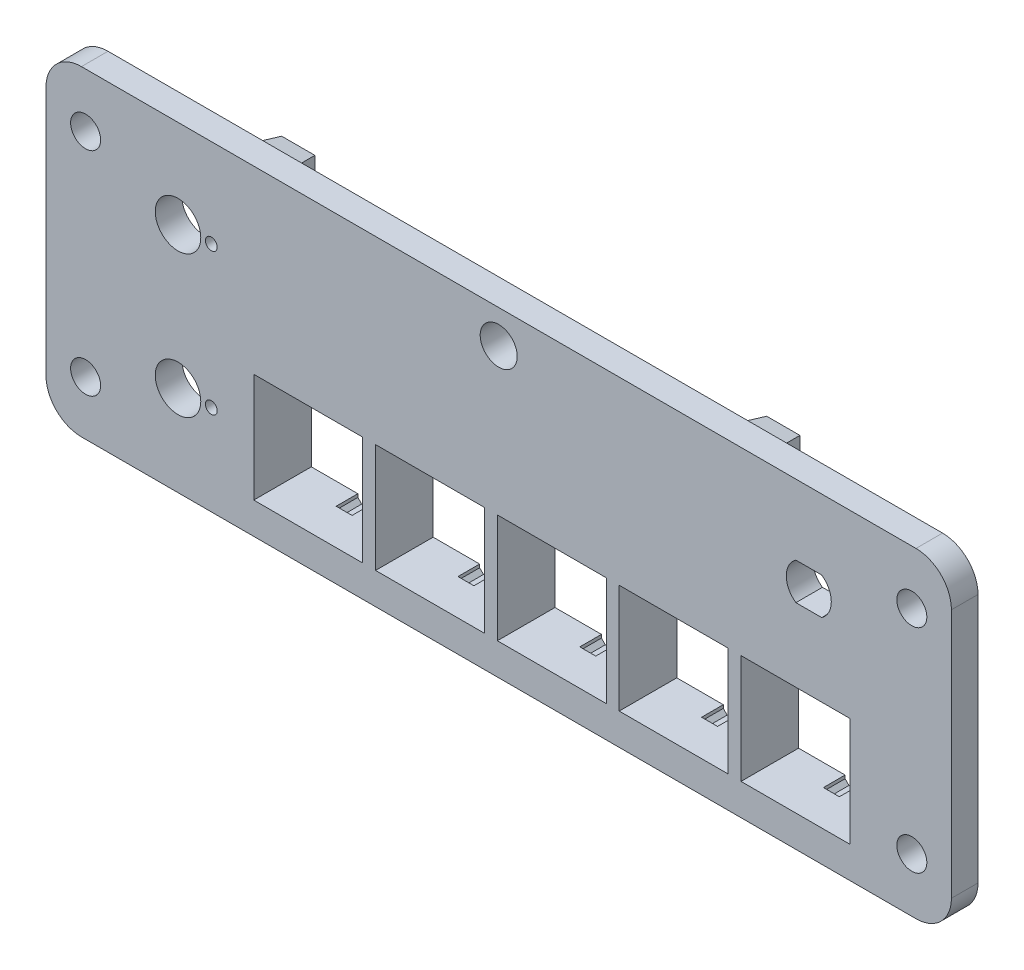
SolidWorks part; units mm, degrees
material "PET"
ref_plane "Front Plane" through (0, 0, 0) normal (0, 0, 1) x (1, 0, 0)
ref_plane "Top Plane" through (0, 0, 0) normal (0, 1, 0) x (1, 0, 0)
ref_plane "Right Plane" through (0, 0, 0) normal (1, 0, 0) x (0, 0, -1)
sketch "Sketch1" plane through (0, 0, 0) normal (0, 0, 1) x (1, 0, 0)
  line L4 (-59.817, -45.974) -> (59.817, -45.974)
  line L5 (64.897, -40.894) -> (64.897, -5.08)
  line L6 (59.817, 0) -> (-59.817, 0)
  line L7 (-64.897, -5.08) -> (-64.897, -40.894)
  line L8 (-59.817, -45.974) -> (59.817, -45.974)
  line L9 (64.897, -40.894) -> (64.897, -5.08)
  line L10 (59.817, 0) -> (-59.817, 0)
  line L11 (-64.897, -5.08) -> (-64.897, -40.894)
  arc A4 (-64.897, -40.894) -> (-59.817, -45.974) centre (-59.817, -40.894) ccw
  arc A5 (59.817, -45.974) -> (64.897, -40.894) centre (59.817, -40.894) ccw
  arc A6 (64.897, -5.08) -> (59.817, 0) centre (59.817, -5.08) ccw
  arc A7 (-59.817, 0) -> (-64.897, -5.08) centre (-59.817, -5.08) ccw
  arc A8 (-64.897, -40.894) -> (-59.817, -45.974) centre (-59.817, -40.894) ccw
  arc A9 (59.817, -45.974) -> (64.897, -40.894) centre (59.817, -40.894) ccw
  arc A10 (64.897, -5.08) -> (59.817, 0) centre (59.817, -5.08) ccw
  arc A11 (-59.817, 0) -> (-64.897, -5.08) centre (-59.817, -5.08) ccw
  dimension "D1" = 0
extrude "Boss-Extrude1" add sketch "Sketch1" along normal blind 3.81
sketch "Sketch5" plane through (0, 0, 3.81) normal (0, 0, 1) x (1, 0, 0)
  line L4 (52.07, -41.91) -> (52.07, -25.4)
  line L5 (50.8, -24.13) -> (-35.56, -24.13)
  line L6 (-36.83, -25.4) -> (-36.83, -41.91)
  line L7 (-35.56, -43.18) -> (50.8, -43.18)
  line L8 (52.07, -41.91) -> (52.07, -25.4)
  line L9 (50.8, -24.13) -> (-35.56, -24.13)
  line L10 (-36.83, -25.4) -> (-36.83, -41.91)
  line L11 (-35.56, -43.18) -> (50.8, -43.18)
  arc A4 (52.07, -25.4) -> (50.8, -24.13) centre (50.8, -25.4) ccw
  arc A5 (-35.56, -24.13) -> (-36.83, -25.4) centre (-35.56, -25.4) ccw
  arc A6 (-36.83, -41.91) -> (-35.56, -43.18) centre (-35.56, -41.91) ccw
  arc A7 (50.8, -43.18) -> (52.07, -41.91) centre (50.8, -41.91) ccw
  arc A8 (52.07, -25.4) -> (50.8, -24.13) centre (50.8, -25.4) ccw
  arc A9 (-35.56, -24.13) -> (-36.83, -25.4) centre (-35.56, -25.4) ccw
  arc A10 (-36.83, -41.91) -> (-35.56, -43.18) centre (-35.56, -41.91) ccw
  arc A11 (50.8, -43.18) -> (52.07, -41.91) centre (50.8, -41.91) ccw
  dimension "D1" = 0
extrude "Cut-Extrude1" cut sketch "Sketch5" against normal through all
hole_wizard "#6 Clearance Hole1" positions "Sketch7" profile "Sketch6" hole size "#6" standard "ANSI Inch" end condition through all
sketch "Sketch7" plane through (0, 0, 3.81) normal (0, 0, 1) x (1, 0, 0)
  point P0 (59.2201, -7.747)
  point P3 (59.2201, -38.227)
  point P6 (-59.2201, -38.227)
  point P9 (-59.2201, -7.747)
sketch "Sketch6" plane through (59.2201, -7.747, 3.81) normal (1, 0, 0) x (0, -1, 0)
  line L0 (0, 0) -> (0, 3.81)
  line L1 (0, 3.81) -> (2.1526, 3.81)
  line L2 (2.1526, 3.81) -> (2.1526, 0)
  line L5 (2.1526, 0) -> (0, 0)
  line L11 (0, -6.35) -> (0, 107.95) construction
  dimension "Thru Hole Dia." = 4.3053
  dimension "Thru Hole Depth" = 3.81
sketch "Sketch8" plane through (0, 0, 3.81) normal (0, 0, 1) x (1, 0, 0)
  line L1 (42.5986, -10.0584) -> (46.3014, -10.0584)
  line L2 (44.45, -15.3416) -> (44.45, -10.0584)
  line L3 (46.3014, -15.3416) -> (42.5986, -15.3416)
  arc A0 (42.5986, -10.0584) -> (42.5986, -15.3416) centre (44.45, -12.7) ccw
  arc A1 (46.3014, -15.3416) -> (46.3014, -10.0584) centre (44.45, -12.7) ccw
  point P9 (44.45, -12.7)
  point P12 (44.45, -15.3416)
  dimension "D1" = 6.4516
  dimension "D2" = 5.2832
extrude "Cut-Extrude2" cut sketch "Sketch8" against normal through all contours L3 A1 L1 L2 | L1 A0 L3 L2
sketch "Sketch9" plane through (0, 0, 3.81) normal (0, 0, 1) x (1, 0, 0)
  line L2 (38.6715, -12.7) -> (50.2285, -12.7) construction
  line L3 (-45.974, -12.7) -> (-45.974, -33.02) construction
  line L4 (44.45, -20.1151) -> (44.45, -5.2849) construction
  line L5 (-45.974, -22.86) -> (-64.897, -22.86) construction
  line L6 (-64.897, -5.08) -> (-64.897, -40.894) construction
  circle A0 centre (-45.974, -12.7) radius 3.2639
  circle A1 centre (-41.1988, -12.7) radius 0.8509
  circle A2 centre (-45.974, -33.02) radius 3.2639
  circle A3 centre (-41.1988, -33.02) radius 0.8509
  circle A4 centre (-45.974, -33.02) radius 3.2639
  point P0 (-45.974, -12.7)
  point P4 (-45.974, -33.02)
  dimension "D1" = 6.5278
  dimension "D2" = 1.7018
  dimension "D3" = 4.7752
extrude "Cut-Extrude3" cut sketch "Sketch9" against normal through all contours A2 | A3 | A0 | A1
hole_wizard "#6-32 Tapped Hole1" positions "Sketch11" profile "Sketch10" tap size "#6-32" standard "ANSI Inch" end condition through all
sketch "Sketch11" plane through (0, 0, 3.81) normal (0, 0, 1) x (1, 0, 0)
  point P0 (0, -4.7575)
sketch "Sketch10" plane through (0, -4.7575, 3.81) normal (1, 0, 0) x (0, -1, 0)
  line L0 (0, 0) -> (0, 3.81)
  line L1 (0, 3.81) -> (1.3525, 3.81)
  line L2 (1.3525, 3.81) -> (1.3525, 0)
  line L5 (1.3525, 0) -> (0, 0)
  line L11 (0, -6.35) -> (0, 107.95) construction
  dimension "Thru Tap Drill Dia." = 2.7051
  dimension "Thru Tap Drill Depth" = 3.81
cosmetic thread "Hole Thread1" parameters "D2"=3.5052
sketch "Sketch12" plane through (0, 0, 3.81) normal (0, 0, 1) x (1, 0, 0)
  line L0 (5.95, -21.748) -> (11.95, -21.748) construction
  line L1 (8.95, -21.748) -> (-9, -21.748)
  line L2 (8.95, -21.748) -> (8.95, -9.748)
  line L3 (8.95, -9.748) -> (-9, -9.748)
  line L4 (-9, -21.748) -> (-9, -9.748)
  line L5 (8.95, -21.748) -> (-9, -9.748) construction
  line L6 (8.95, -9.748) -> (-9, -21.748) construction
  line L7 (-9, -22.748) -> (-9, -8.748) construction
  line L11 (5.95, -9.748) -> (-5.95, -9.748) construction
  point P4 (-0.025, -15.748)
extrude "Cut-Extrude4" [suppressed] cut sketch "Sketch12" against normal through all
fillet "Fillet1" [suppressed] radius 1.651
hole_wizard "CSK for #4 Flat Head Machine Screw (100)1" [suppressed] positions "Sketch14" profile "Sketch13" countersink size "#4" standard "ANSI Inch"
sketch "Sketch14" plane through (0, 0, 3.175) normal (0, 0, 1) x (1, 0, 0)
  point P0 (-15, -15.748)
  point P3 (15, -15.748)
sketch "Sketch13" plane through (-15, -15.748, 3.175) normal (1, 0, 0) x (0, -1, 0)
  line L0 (0, 0) -> (0, 3.175)
  line L1 (0, 3.175) -> (1.7272, 3.175)
  line L2 (1.7272, 3.175) -> (1.7272, 1.2024)
  line L3 (1.7272, 1.2024) -> (3.1602, 0)
  line L5 (3.1602, 0) -> (0, 0)
  line L6 (-1.7272, 1.2024) -> (-3.1602, 0) construction
  line L11 (0, -6.35) -> (0, 107.95) construction
  dimension "Thru Hole Dia." = 3.4544
  dimension "Thru Hole Depth" = 3.175
  dimension "Near C'Sink Dia." = 6.3204
  dimension "Near C'Sink Angle" = 100
sketch "Sketch15" plane through (0, 0, 3.81) normal (0, 0, 1) x (1, 0, 0)
  line L0 (44.45, -12.7) -> (44.45, -18.415) construction
  line L1 (44.45, -18.415) -> (44.45, -19.177) construction
  line L2 (47.8092, -17.3235) -> (48.2571, -17.94) construction
  line L3 (44.45, -12.7) -> (47.8092, -17.3235) construction
  line L4 (49.8853, -14.466) -> (50.61, -14.7015) construction
  line L5 (44.45, -12.7) -> (49.8853, -14.466) construction
  line L6 (49.8853, -10.934) -> (50.61, -10.6985) construction
  line L7 (44.45, -12.7) -> (49.8853, -10.934) construction
  line L8 (47.8092, -8.0765) -> (48.2571, -7.46) construction
  line L9 (44.45, -12.7) -> (47.8092, -8.0765) construction
  line L10 (44.45, -12.7) -> (44.45, -18.415) construction
  line L11 (44.45, -12.7) -> (47.8092, -17.3235) construction
  line L12 (48.2571, -17.94) -> (50.2891, -17.94) construction
  line L16 (48.2571, -5.8306) -> (50.2891, -5.8306) construction
  line L17 (52.642, -9.655) -> (50.61, -9.655) construction
  line L18 (50.61, -13.8984) -> (52.642, -13.8984) construction
  line L19 (45.3869, -19.177) -> (43.5131, -19.177) construction
  line L20 (44.45, -12.7) -> (44.45, -21.7325) construction
  line L21 (52.467, -21.7325) -> (36.433, -21.7325) construction
  line L22 (-45.974, -33.02) -> (-45.974, -40.64) construction
  line L23 (-45.974, -38.735) -> (-45.974, -27.305) construction
  line L24 (-40.2446, -40.64) -> (-51.7034, -40.64) construction
  line L25 (-45.974, -12.7) -> (-45.974, -20.32) construction
  line L26 (-45.974, -18.415) -> (-45.974, -6.985) construction
  line L27 (-39.5334, -20.32) -> (-52.4146, -20.32) construction
  arc A0 (42.684, -18.1353) -> (46.216, -7.2647) centre (44.45, -12.7) ccw construction
  text T0 "F" font "GordonURWCon" height in points 9
  text T1 "U" font "GordonURWCon" height in points 9
  text T2 "A" font "GordonURWCon" height in points 9
  text T3 "I" font "GordonURWCon" height in points 9
  text T4 "N" font "GordonURWCon" height in points 9
  text T5 "DIS TYPE" font "GordonURWMed" height in points 9
  text T6 "AUDIO" font "GordonURWMed" height in points 12
  text T7 "DMR" font "GordonURWMed" height in points 12
  point P23 (49.2731, -17.94)
  point P33 (44.45, -21.7325)
  point P43 (44.45, -19.177)
  point P45 (-45.974, -40.64)
  point P54 (-45.974, -20.32)
  dimension "D1" = 5
  dimension "D4" = 7.62
  dimension "D5" = 0.762
  dimension "D2" = 36
  dimension "D3" = 2.032
wrap "Wrap1" [suppressed] sketch "Sketch15" source sketch "Sketch15"
sketch "Sketch16" plane through (0, 0, 3.81) normal (0, 0, 1) x (1, 0, 0)
  line L0 (11.2625, -24.13) -> (16.025, -24.13) construction
  line L1 (13.6437, -24.13) -> (13.6437, -19.3675) construction
  line L2 (7.1437, -43.18) -> (7.1437, -2.54) construction
  line L3 (-39.37, -2.54) -> (34.925, -2.54) construction
  line L9 (50.3555, -41.4655) -> (50.3555, -25.8445)
  line L10 (50.3555, -25.8445) -> (34.7345, -25.8445)
  line L11 (34.7345, -25.8445) -> (34.7345, -41.4655)
  line L12 (34.7345, -41.4655) -> (50.3555, -41.4655)
  line L13 (50.3555, -41.4655) -> (50.3555, -25.8445)
  line L14 (50.3555, -25.8445) -> (34.7345, -25.8445)
  line L15 (34.7345, -25.8445) -> (34.7345, -41.4655)
  line L16 (34.7345, -41.4655) -> (50.3555, -41.4655)
  line L17 (-2.032, -41.4655) -> (-2.032, -25.8445)
  line L18 (-2.032, -25.8445) -> (-17.653, -25.8445)
  line L19 (-17.653, -25.8445) -> (-17.653, -41.4655)
  line L20 (-17.653, -41.4655) -> (-2.032, -41.4655)
  line L21 (-2.032, -41.4655) -> (-2.032, -25.8445)
  line L22 (32.893, -41.4655) -> (32.893, -25.8445)
  line L23 (32.893, -25.8445) -> (17.272, -25.8445)
  line L24 (17.272, -25.8445) -> (17.272, -41.4655)
  line L25 (17.272, -41.4655) -> (32.893, -41.4655)
  line L26 (32.893, -41.4655) -> (32.893, -25.8445)
  line L27 (32.893, -25.8445) -> (17.272, -25.8445)
  line L28 (17.272, -25.8445) -> (17.272, -41.4655)
  line L29 (17.272, -41.4655) -> (32.893, -41.4655)
  line L30 (-2.032, -25.8445) -> (-17.653, -25.8445)
  line L31 (-17.653, -25.8445) -> (-17.653, -41.4655)
  line L32 (-17.653, -41.4655) -> (-2.032, -41.4655)
  line L34 (-39.37, -43.18) -> (-39.37, -2.54) construction
  line L35 (15.4305, -41.4655) -> (15.4305, -25.8445)
  line L36 (15.4305, -25.8445) -> (-0.1905, -25.8445)
  line L37 (-0.1905, -25.8445) -> (-0.1905, -41.4655)
  line L38 (-0.1905, -41.4655) -> (15.4305, -41.4655)
  line L39 (15.4305, -41.4655) -> (15.4305, -25.8445)
  line L40 (15.4305, -25.8445) -> (-0.1905, -25.8445)
  line L41 (-0.1905, -25.8445) -> (-0.1905, -41.4655)
  line L42 (-0.1905, -41.4655) -> (15.4305, -41.4655)
  line L43 (-39.37, -43.18) -> (53.6575, -43.18)
  line L44 (-39.37, -43.18) -> (-39.37, -24.13)
  line L45 (-39.37, -24.13) -> (11.2625, -24.13)
  line L46 (-19.4945, -41.4655) -> (-19.4945, -25.8445)
  line L47 (-19.4945, -25.8445) -> (-35.1155, -25.8445)
  line L48 (-35.1155, -25.8445) -> (-35.1155, -41.4655)
  line L49 (-35.1155, -41.4655) -> (-19.4945, -41.4655)
  line L50 (-19.4945, -41.4655) -> (-19.4945, -25.8445)
  line L51 (-19.4945, -25.8445) -> (-35.1155, -25.8445)
  line L52 (-35.1155, -25.8445) -> (-35.1155, -41.4655)
  line L53 (-35.1155, -41.4655) -> (-19.4945, -41.4655)
  line L54 (53.6575, -43.18) -> (53.6575, -24.13)
  line L55 (53.6575, -24.13) -> (53.6575, -43.18) construction
  line L56 (44.925, -24.13) -> (53.6575, -24.13) construction
  line L57 (53.6575, -43.18) -> (-39.37, -43.18) construction
  line L58 (16.025, -24.13) -> (53.6575, -24.13)
  line L59 (34.925, -2.54) -> (30.1625, -2.54)
  line L60 (34.925, -2.54) -> (34.925, -7.3025)
  line L61 (34.925, -7.3025) -> (30.1625, -7.3025)
  line L62 (30.1625, -2.54) -> (30.1625, -7.3025)
  line L63 (-39.37, -2.54) -> (-34.6075, -2.54)
  line L64 (-39.37, -2.54) -> (-39.37, -7.3025)
  line L65 (-39.37, -7.3025) -> (-34.6075, -7.3025)
  line L66 (-34.6075, -2.54) -> (-34.6075, -7.3025)
  line L67 (11.2625, -19.3675) -> (16.025, -19.3675)
  line L68 (11.2625, -19.3675) -> (11.2625, -24.13)
  line L70 (16.025, -19.3675) -> (16.025, -24.13)
  dimension "D6" = 4.7625
  dimension "D7" = 6.5
  dimension "D1" = 0.762
  dimension "D2" = 0.762
  dimension "D3" = 0.762
  dimension "D4" = 0.762
  dimension "D5" = 0.762
extrude "Boss-Extrude2" add sketch "Sketch16" against normal up to surface (8.255 mm away) contours L68 L45 L44 L43 L54 L58 L70 L67
sketch "Sketch17" plane through (0, 0, -4.445) normal (0, 0, -1) x (-1, 0, 0)
  line L44 (-37.8778, -26.0985) -> (-37.8778, -25.3801)
  line L45 (-37.8778, -25.3801) -> (-38.4293, -24.8285)
  line L46 (-38.4293, -24.8285) -> (-39.6122, -24.8285)
  line L47 (-39.6122, -24.8285) -> (-40.1638, -25.3801)
  line L48 (-40.1638, -25.3801) -> (-40.1638, -26.0985)
  line L49 (-40.1638, -26.0985) -> (-44.9263, -26.0985)
  line L50 (-44.9263, -26.0985) -> (-44.9263, -25.3801)
  line L51 (-44.9263, -25.3801) -> (-45.4778, -24.8285)
  line L52 (-45.4778, -24.8285) -> (-46.6607, -24.8285)
  line L53 (-46.6607, -24.8285) -> (-47.2123, -25.3801)
  line L54 (-47.2123, -25.3801) -> (-47.2123, -26.0985)
  line L55 (-47.2123, -26.0985) -> (-50.1015, -26.0985)
  line L56 (-50.1015, -26.0985) -> (-50.1015, -41.2115)
  line L57 (-50.1015, -41.2115) -> (-43.688, -41.2115)
  line L58 (-43.688, -41.2115) -> (-43.688, -41.9299)
  line L59 (-43.688, -41.9299) -> (-43.1364, -42.4815)
  line L60 (-43.1364, -42.4815) -> (-41.9536, -42.4815)
  line L61 (-41.9536, -42.4815) -> (-41.402, -41.9299)
  line L62 (-41.402, -41.9299) -> (-41.402, -41.2115)
  line L63 (-41.402, -41.2115) -> (-34.9885, -41.2115)
  line L64 (-34.9885, -41.2115) -> (-34.9885, -26.0985)
  line L65 (-34.9885, -26.0985) -> (-37.8778, -26.0985)
  line L66 (-37.8778, -26.0985) -> (-37.8778, -25.3801)
  line L67 (-37.8778, -25.3801) -> (-38.4293, -24.8285)
  line L68 (-38.4293, -24.8285) -> (-39.6122, -24.8285)
  line L69 (-39.6122, -24.8285) -> (-40.1638, -25.3801)
  line L70 (-40.1638, -25.3801) -> (-40.1638, -26.0985)
  line L71 (-40.1638, -26.0985) -> (-44.9263, -26.0985)
  line L72 (-44.9263, -26.0985) -> (-44.9263, -25.3801)
  line L73 (-44.9263, -25.3801) -> (-45.4778, -24.8285)
  line L74 (-45.4778, -24.8285) -> (-46.6607, -24.8285)
  line L75 (-46.6607, -24.8285) -> (-47.2123, -25.3801)
  line L76 (-47.2123, -25.3801) -> (-47.2123, -26.0985)
  line L77 (-47.2123, -26.0985) -> (-50.1015, -26.0985)
  line L78 (-50.1015, -26.0985) -> (-50.1015, -41.2115)
  line L79 (-50.1015, -41.2115) -> (-43.688, -41.2115)
  line L80 (-43.688, -41.2115) -> (-43.688, -41.9299)
  line L81 (-43.688, -41.9299) -> (-43.1364, -42.4815)
  line L82 (-43.1364, -42.4815) -> (-41.9536, -42.4815)
  line L83 (-41.9536, -42.4815) -> (-41.402, -41.9299)
  line L84 (-41.402, -41.9299) -> (-41.402, -41.2115)
  line L85 (-41.402, -41.2115) -> (-34.9885, -41.2115)
  line L86 (-34.9885, -41.2115) -> (-34.9885, -26.0985)
  line L87 (-34.9885, -26.0985) -> (-37.8778, -26.0985)
  line L88 (14.5097, -26.0985) -> (14.5097, -25.3801)
  line L89 (14.5097, -25.3801) -> (13.9582, -24.8285)
  line L90 (13.9582, -24.8285) -> (12.7753, -24.8285)
  line L91 (12.7753, -24.8285) -> (12.2237, -25.3801)
  line L92 (12.2237, -25.3801) -> (12.2237, -26.0985)
  line L93 (12.2237, -26.0985) -> (7.4612, -26.0985)
  line L94 (7.4612, -26.0985) -> (7.4612, -25.3801)
  line L95 (7.4612, -25.3801) -> (6.9097, -24.8285)
  line L96 (6.9097, -24.8285) -> (5.7268, -24.8285)
  line L97 (5.7268, -24.8285) -> (5.1752, -25.3801)
  line L98 (5.1752, -25.3801) -> (5.1752, -26.0985)
  line L99 (5.1752, -26.0985) -> (2.286, -26.0985)
  line L100 (2.286, -26.0985) -> (2.286, -41.2115)
  line L101 (2.286, -41.2115) -> (8.6995, -41.2115)
  line L102 (8.6995, -41.2115) -> (8.6995, -41.9299)
  line L103 (8.6995, -41.9299) -> (9.2511, -42.4815)
  line L104 (9.2511, -42.4815) -> (10.4339, -42.4815)
  line L105 (10.4339, -42.4815) -> (10.9855, -41.9299)
  line L106 (10.9855, -41.9299) -> (10.9855, -41.2115)
  line L107 (10.9855, -41.2115) -> (17.399, -41.2115)
  line L108 (17.399, -41.2115) -> (17.399, -26.0985)
  line L109 (17.399, -26.0985) -> (14.5097, -26.0985)
  line L110 (-20.4153, -26.0985) -> (-20.4153, -25.3801)
  line L111 (-20.4153, -25.3801) -> (-20.9668, -24.8285)
  line L112 (-20.9668, -24.8285) -> (-22.1497, -24.8285)
  line L113 (-22.1497, -24.8285) -> (-22.7013, -25.3801)
  line L114 (-22.7013, -25.3801) -> (-22.7013, -26.0985)
  line L115 (-22.7013, -26.0985) -> (-27.4638, -26.0985)
  line L116 (-27.4638, -26.0985) -> (-27.4638, -25.3801)
  line L117 (-27.4638, -25.3801) -> (-28.0153, -24.8285)
  line L118 (-28.0153, -24.8285) -> (-29.1982, -24.8285)
  line L119 (-29.1982, -24.8285) -> (-29.7498, -25.3801)
  line L120 (-29.7498, -25.3801) -> (-29.7498, -26.0985)
  line L121 (-29.7498, -26.0985) -> (-32.639, -26.0985)
  line L122 (-32.639, -26.0985) -> (-32.639, -41.2115)
  line L123 (-32.639, -41.2115) -> (-26.2255, -41.2115)
  line L124 (-26.2255, -41.2115) -> (-26.2255, -41.9299)
  line L125 (-26.2255, -41.9299) -> (-25.6739, -42.4815)
  line L126 (-25.6739, -42.4815) -> (-24.4911, -42.4815)
  line L127 (-24.4911, -42.4815) -> (-23.9395, -41.9299)
  line L128 (-23.9395, -41.9299) -> (-23.9395, -41.2115)
  line L129 (-23.9395, -41.2115) -> (-17.526, -41.2115)
  line L130 (-17.526, -41.2115) -> (-17.526, -26.0985)
  line L131 (-17.526, -26.0985) -> (-20.4153, -26.0985)
  line L132 (-20.4153, -26.0985) -> (-20.4153, -25.3801)
  line L133 (-20.4153, -25.3801) -> (-20.9668, -24.8285)
  line L134 (-20.9668, -24.8285) -> (-22.1497, -24.8285)
  line L135 (-22.1497, -24.8285) -> (-22.7013, -25.3801)
  line L136 (-22.7013, -25.3801) -> (-22.7013, -26.0985)
  line L137 (-22.7013, -26.0985) -> (-27.4638, -26.0985)
  line L138 (-27.4638, -26.0985) -> (-27.4638, -25.3801)
  line L139 (-27.4638, -25.3801) -> (-28.0153, -24.8285)
  line L140 (-28.0153, -24.8285) -> (-29.1982, -24.8285)
  line L141 (-29.1982, -24.8285) -> (-29.7498, -25.3801)
  line L142 (-29.7498, -25.3801) -> (-29.7498, -26.0985)
  line L143 (-29.7498, -26.0985) -> (-32.639, -26.0985)
  line L144 (-32.639, -26.0985) -> (-32.639, -41.2115)
  line L145 (-32.639, -41.2115) -> (-26.2255, -41.2115)
  line L146 (-26.2255, -41.2115) -> (-26.2255, -41.9299)
  line L147 (-26.2255, -41.9299) -> (-25.6739, -42.4815)
  line L148 (-25.6739, -42.4815) -> (-24.4911, -42.4815)
  line L149 (-24.4911, -42.4815) -> (-23.9395, -41.9299)
  line L150 (-23.9395, -41.9299) -> (-23.9395, -41.2115)
  line L151 (-23.9395, -41.2115) -> (-17.526, -41.2115)
  line L152 (-17.526, -41.2115) -> (-17.526, -26.0985)
  line L153 (-17.526, -26.0985) -> (-20.4153, -26.0985)
  line L176 (-2.9528, -26.0985) -> (-2.9528, -25.3801)
  line L177 (-2.9528, -25.3801) -> (-3.5043, -24.8285)
  line L178 (-3.5043, -24.8285) -> (-4.6872, -24.8285)
  line L179 (-4.6872, -24.8285) -> (-5.2388, -25.3801)
  line L180 (-5.2388, -25.3801) -> (-5.2388, -26.0985)
  line L181 (-5.2388, -26.0985) -> (-10.0013, -26.0985)
  line L182 (-10.0013, -26.0985) -> (-10.0013, -25.3801)
  line L183 (-10.0013, -25.3801) -> (-10.5528, -24.8285)
  line L184 (-10.5528, -24.8285) -> (-11.7357, -24.8285)
  line L185 (-11.7357, -24.8285) -> (-12.2873, -25.3801)
  line L186 (-12.2873, -25.3801) -> (-12.2873, -26.0985)
  line L187 (-12.2873, -26.0985) -> (-15.1765, -26.0985)
  line L188 (-15.1765, -26.0985) -> (-15.1765, -41.2115)
  line L189 (-15.1765, -41.2115) -> (-8.763, -41.2115)
  line L190 (-8.763, -41.2115) -> (-8.763, -41.9299)
  line L191 (-8.763, -41.9299) -> (-8.2114, -42.4815)
  line L192 (-8.2114, -42.4815) -> (-7.0286, -42.4815)
  line L193 (-7.0286, -42.4815) -> (-6.477, -41.9299)
  line L194 (-6.477, -41.9299) -> (-6.477, -41.2115)
  line L195 (-6.477, -41.2115) -> (-0.0635, -41.2115)
  line L196 (-0.0635, -41.2115) -> (-0.0635, -26.0985)
  line L197 (-0.0635, -26.0985) -> (-2.9528, -26.0985)
  line L198 (-2.9528, -26.0985) -> (-2.9528, -25.3801)
  line L199 (-2.9528, -25.3801) -> (-3.5043, -24.8285)
  line L200 (-3.5043, -24.8285) -> (-4.6872, -24.8285)
  line L201 (-4.6872, -24.8285) -> (-5.2388, -25.3801)
  line L202 (-5.2388, -25.3801) -> (-5.2388, -26.0985)
  line L203 (-5.2388, -26.0985) -> (-10.0013, -26.0985)
  line L204 (-10.0013, -26.0985) -> (-10.0013, -25.3801)
  line L205 (-10.0013, -25.3801) -> (-10.5528, -24.8285)
  line L206 (-10.5528, -24.8285) -> (-11.7357, -24.8285)
  line L207 (-11.7357, -24.8285) -> (-12.2873, -25.3801)
  line L208 (-12.2873, -25.3801) -> (-12.2873, -26.0985)
  line L209 (-12.2873, -26.0985) -> (-15.1765, -26.0985)
  line L210 (-15.1765, -26.0985) -> (-15.1765, -41.2115)
  line L211 (-15.1765, -41.2115) -> (-8.763, -41.2115)
  line L212 (-8.763, -41.2115) -> (-8.763, -41.9299)
  line L213 (-8.763, -41.9299) -> (-8.2114, -42.4815)
  line L214 (-8.2114, -42.4815) -> (-7.0286, -42.4815)
  line L215 (-7.0286, -42.4815) -> (-6.477, -41.9299)
  line L216 (-6.477, -41.9299) -> (-6.477, -41.2115)
  line L217 (-6.477, -41.2115) -> (-0.0635, -41.2115)
  line L218 (-0.0635, -41.2115) -> (-0.0635, -26.0985)
  line L219 (-0.0635, -26.0985) -> (-2.9528, -26.0985)
  line L220 (14.5097, -26.0985) -> (14.5097, -25.3801)
  line L221 (14.5097, -25.3801) -> (13.9582, -24.8285)
  line L222 (13.9582, -24.8285) -> (12.7753, -24.8285)
  line L223 (12.7753, -24.8285) -> (12.2237, -25.3801)
  line L224 (12.2237, -25.3801) -> (12.2237, -26.0985)
  line L225 (12.2237, -26.0985) -> (7.4612, -26.0985)
  line L226 (7.4612, -26.0985) -> (7.4612, -25.3801)
  line L227 (7.4612, -25.3801) -> (6.9097, -24.8285)
  line L228 (6.9097, -24.8285) -> (5.7268, -24.8285)
  line L229 (5.7268, -24.8285) -> (5.1752, -25.3801)
  line L230 (5.1752, -25.3801) -> (5.1752, -26.0985)
  line L231 (5.1752, -26.0985) -> (2.286, -26.0985)
  line L232 (2.286, -26.0985) -> (2.286, -41.2115)
  line L233 (2.286, -41.2115) -> (8.6995, -41.2115)
  line L234 (8.6995, -41.2115) -> (8.6995, -41.9299)
  line L235 (8.6995, -41.9299) -> (9.2511, -42.4815)
  line L236 (9.2511, -42.4815) -> (10.4339, -42.4815)
  line L237 (10.4339, -42.4815) -> (10.9855, -41.9299)
  line L238 (10.9855, -41.9299) -> (10.9855, -41.2115)
  line L239 (10.9855, -41.2115) -> (17.399, -41.2115)
  line L240 (17.399, -41.2115) -> (17.399, -26.0985)
  line L241 (17.399, -26.0985) -> (14.5097, -26.0985)
  line L264 (31.9722, -26.0985) -> (31.9722, -25.3801)
  line L265 (31.9722, -25.3801) -> (31.4207, -24.8285)
  line L266 (31.4207, -24.8285) -> (30.2378, -24.8285)
  line L267 (30.2378, -24.8285) -> (29.6862, -25.3801)
  line L268 (29.6862, -25.3801) -> (29.6862, -26.0985)
  line L269 (29.6862, -26.0985) -> (24.9237, -26.0985)
  line L270 (24.9237, -26.0985) -> (24.9237, -25.3801)
  line L271 (24.9237, -25.3801) -> (24.3722, -24.8285)
  line L272 (24.3722, -24.8285) -> (23.1893, -24.8285)
  line L273 (23.1893, -24.8285) -> (22.6377, -25.3801)
  line L274 (22.6377, -25.3801) -> (22.6377, -26.0985)
  line L275 (22.6377, -26.0985) -> (19.7485, -26.0985)
  line L276 (19.7485, -26.0985) -> (19.7485, -41.2115)
  line L277 (19.7485, -41.2115) -> (26.162, -41.2115)
  line L278 (26.162, -41.2115) -> (26.162, -41.9299)
  line L279 (26.162, -41.9299) -> (26.7136, -42.4815)
  line L280 (26.7136, -42.4815) -> (27.8964, -42.4815)
  line L281 (27.8964, -42.4815) -> (28.448, -41.9299)
  line L282 (28.448, -41.9299) -> (28.448, -41.2115)
  line L283 (28.448, -41.2115) -> (34.8615, -41.2115)
  line L284 (34.8615, -41.2115) -> (34.8615, -26.0985)
  line L285 (34.8615, -26.0985) -> (31.9722, -26.0985)
  line L286 (31.9722, -26.0985) -> (31.9722, -25.3801)
  line L287 (31.9722, -25.3801) -> (31.4207, -24.8285)
  line L288 (31.4207, -24.8285) -> (30.2378, -24.8285)
  line L289 (30.2378, -24.8285) -> (29.6862, -25.3801)
  line L290 (29.6862, -25.3801) -> (29.6862, -26.0985)
  line L291 (29.6862, -26.0985) -> (24.9237, -26.0985)
  line L292 (24.9237, -26.0985) -> (24.9237, -25.3801)
  line L293 (24.9237, -25.3801) -> (24.3722, -24.8285)
  line L294 (24.3722, -24.8285) -> (23.1893, -24.8285)
  line L295 (23.1893, -24.8285) -> (22.6377, -25.3801)
  line L296 (22.6377, -25.3801) -> (22.6377, -26.0985)
  line L297 (22.6377, -26.0985) -> (19.7485, -26.0985)
  line L298 (19.7485, -26.0985) -> (19.7485, -41.2115)
  line L299 (19.7485, -41.2115) -> (26.162, -41.2115)
  line L300 (26.162, -41.2115) -> (26.162, -41.9299)
  line L301 (26.162, -41.9299) -> (26.7136, -42.4815)
  line L302 (26.7136, -42.4815) -> (27.8964, -42.4815)
  line L303 (27.8964, -42.4815) -> (28.448, -41.9299)
  line L304 (28.448, -41.9299) -> (28.448, -41.2115)
  line L305 (28.448, -41.2115) -> (34.8615, -41.2115)
  line L306 (34.8615, -41.2115) -> (34.8615, -26.0985)
  line L307 (34.8615, -26.0985) -> (31.9722, -26.0985)
  dimension "D1" = 0.508
  dimension "D2" = 0.508
  dimension "D3" = 0.508
  dimension "D4" = 0.508
  dimension "D5" = 0.508
extrude "Cut-Extrude5" cut sketch "Sketch17" against normal up to surface (3.1115 mm away)
hole_wizard "Hole1" positions "Sketch18" profile "Sketch19" legacy
sketch "Sketch18" plane through (0, 0, -4.445) normal (0, 0, -1) x (-1, 0, 0)
  line L0 (-16.025, -24.13) -> (-11.2625, -19.3675) construction
  line L1 (-11.2625, -19.3675) -> (-16.025, -19.3675) construction
  line L2 (-11.2625, -24.13) -> (-11.2625, -19.3675) construction
  line L3 (39.37, -7.3025) -> (34.6075, -2.54) construction
  line L5 (-30.1625, -7.3025) -> (-34.925, -2.54) construction
  line L7 (35.1155, -33.655) -> (39.37, -33.655) construction
  line L8 (35.1155, -41.4655) -> (35.1155, -25.8445) construction
  line L9 (39.37, -43.18) -> (39.37, -24.13) construction
  point P10 (-13.6437, -21.7487)
  point P31 (37.2427, -33.655)
  point P33 (36.9887, -4.9212)
  point P35 (-32.5438, -4.9212)
sketch "Sketch19" plane through (32.5438, -4.9212, -4.445) normal (1, 0, 0) x (0, 1, 0)
  line L0 (0, 0) -> (0, 2.921)
  line L1 (0, 2.921) -> (1.4986, 2.921)
  line L2 (1.4986, 2.921) -> (1.6383, 0)
  line L3 (1.6383, 0) -> (0, 0)
  line L4 (0, 110) -> (0, -10) construction
  dimension "Minor Diameter" = 2.9972
  dimension "Depth" = 2.921
  dimension "Major Diameter" = 3.2766
hole_wizard "Hole2" positions "Sketch20" profile "Sketch21" legacy
sketch "Sketch20" plane through (0, 0, 3.81) normal (0, 0, 1) x (1, 0, 0)
  point P0 (0, -4.7575)
sketch "Sketch21" plane through (0, -4.7575, 3.81) normal (1, 0, 0) x (0, -1, 0)
  line L0 (0, 0) -> (0, 3.81)
  line L1 (0, 3.81) -> (2.5273, 3.81)
  line L2 (2.5273, 3.81) -> (2.6543, 0)
  line L3 (2.6543, 0) -> (0, 0)
  line L4 (0, 110) -> (0, -10) construction
  dimension "Minor Diameter" = 5.0546
  dimension "Depth" = 3.81
  dimension "Major Diameter" = 5.3086
hole_wizard "#2 Clearance Hole1" positions "Sketch22" profile "Sketch23" hole size "#2" standard "ANSI Inch"
sketch "Sketch22" plane through (0, 0, -1.524) normal (0, 0, -1) x (-1, 0, 0)
  point P0 (37.2427, -33.655)
  point P3 (36.9887, -4.9212)
  point P6 (-13.6437, -21.7487)
  point P9 (-32.5438, -4.9212)
sketch "Sketch23" plane through (-37.2427, -33.655, -1.524) normal (1, 0, 0) x (0, 1, 0)
  line L0 (0, 0) -> (0, 3.302)
  line L1 (0, 3.302) -> (1.1303, 3.302)
  line L2 (1.1303, 3.302) -> (1.1303, 0)
  line L5 (1.1303, 0) -> (0, 0)
  line L10 (0, 3.302) -> (-1.1303, 3.302) construction
  line L11 (0, -6.35) -> (0, 107.95) construction
  dimension "Hole Dia." = 2.2606
  dimension "Hole Depth" = 3.302
  dimension "Drill Angle" = 180
draft "Draft1" type of draft neutral plane draft angle 10 faces to draft 7 face at (53.6575, -33.655, -2.2225) face at (34.8412, -24.13, -2.2225) face at (-39.37, -33.655, -2.2225) face at (-14.0538, -24.13, -2.2225) face at (11.2625, -21.7487, -2.2225) face at (13.6437, -19.3675, -2.2225) face at (16.025, -21.7487, -2.2225) neutral plane through (-31.5217, -36.6712, -4.445) neutral plane normal (0, 0, -1) parameters "D1"=10
draft "Draft2" type of draft neutral plane draft angle 10 faces to draft 1 face at (7.1437, -43.18, -2.2225) neutral plane through (-31.5217, -36.6712, -4.445) neutral plane normal (0, 0, -1) parameters "D1"=10
draft "Draft3" type of draft neutral plane draft angle 10 faces to draft 8 face at (32.5438, -2.54, -2.2225) face at (34.925, -4.9212, -2.2225) face at (32.5438, -7.3025, -2.2225) face at (30.1625, -4.9212, -2.2225) face at (-36.9887, -7.3025, -2.2225) face at (-39.37, -4.9212, -2.2225) face at (-36.9887, -2.54, -2.2225) face at (-34.6075, -4.9212, -2.2225) neutral plane through (-31.5217, -36.6712, -4.445) neutral plane normal (0, 0, -1) parameters "D1"=10
